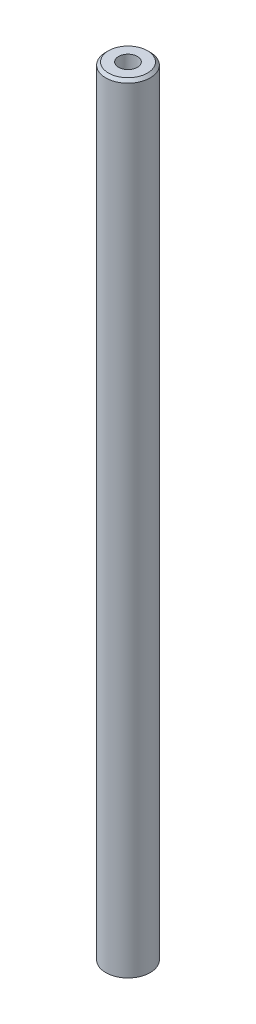
SolidWorks part; units mm, degrees
material "AISI Type 316L stainless steel"
ref_plane "Front Plane" through (0, 0, 0) normal (0, 0, 1) x (1, 0, 0)
ref_plane "Top Plane" through (0, 0, 0) normal (0, 1, 0) x (1, 0, 0)
ref_plane "Right Plane" through (0, 0, 0) normal (1, 0, 0) x (0, 0, -1)
sketch "Sketch1" plane through (0, 0, 0) normal (0, 1, 0) x (1, 0, 0)
  circle A0 centre (0, 0) radius 8
  dimension "D1" = 16
extrude "Boss-Extrude1" add sketch "Sketch1" along normal mid plane 280
hole_wizard "M8 Tapped Hole1" positions "Sketch2" profile "Sketch3" tap size "M8" standard "ISO"
sketch "Sketch2" plane through (0, 140, 0) normal (0, 1, 0) x (1, 0, 0)
  point P0 (0, 0)
sketch "Sketch3" plane through (0, 140, 0) normal (1, 0, 0) x (0, 0, 1)
  line L0 (0, 0) -> (0, 21.7929)
  line L1 (0, 21.7929) -> (3.4, 19.75)
  line L2 (3.4, 19.75) -> (3.4, 0)
  line L5 (3.4, 0) -> (0, 0)
  line L10 (0, 21.7929) -> (-3.4, 19.75) construction
  line L11 (0, -6.35) -> (0, 107.95) construction
  dimension "Tap Drill Dia." = 6.8
  dimension "Tap Drill Depth" = 19.75
  dimension "Drill Angle" = 118
cosmetic thread "Hole Thread1" parameters "D1"=16, "D2"=8
chamfer "Chamfer1" distance 1 angle 45 1 edges at (0, 140, 8)
